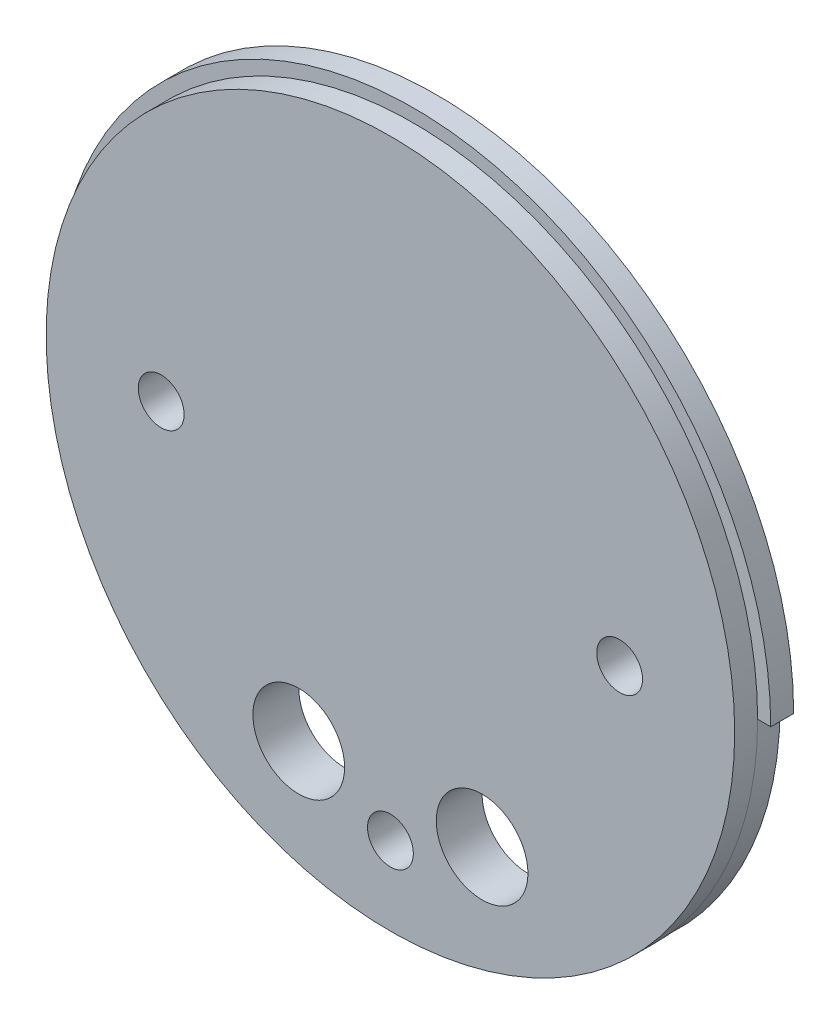
SolidWorks part; units mm, degrees
ref_plane "Front Plane" through (0, 0, 0) normal (0, 0, 1) x (1, 0, 0)
ref_plane "Top Plane" through (0, 0, 0) normal (0, 1, 0) x (1, 0, 0)
ref_plane "Right Plane" through (0, 0, 0) normal (1, 0, 0) x (0, 0, -1)
sketch "Sketch1" plane through (0, 0, 0) normal (0, 0, 1) x (1, 0, 0)
  circle A0 centre (0, 0) radius 49.5046
  dimension "D1" = 99.0092
extrude "Boss-Extrude1" add sketch "Sketch1" along normal blind 3.175
sketch "Sketch2" plane through (0, 0, 3.175) normal (0, 0, 1) x (1, 0, 0)
  circle A0 centre (0, 0) radius 47.6885
  dimension "D1" = 95.377
extrude "Boss-Extrude2" add sketch "Sketch2" along normal blind 3.175
sketch "Sketch3" plane through (0, 0, 6.35) normal (0, 0, 1) x (1, 0, 0)
  line L0 (-7.9375, -31.2354) -> (7.9375, -31.2354) construction
  circle A0 centre (-31.75, 0) radius 3.175
  circle A1 centre (31.75, 0) radius 3.175
  circle A2 centre (-12.7, -31.2354) radius 6.35
  circle A3 centre (-12.7, -31.2354) radius 13.97 construction
  circle A4 centre (-12.7, -31.2354) radius 4.7625 construction
  circle A5 centre (0, 0) radius 47.6885 construction
  circle A6 centre (12.7, -31.2354) radius 6.35
  circle A7 centre (12.7, -31.2354) radius 13.97 construction
  circle A8 centre (-12.7, -31.2354) radius 12.7 construction
  circle A9 centre (12.7, -31.2354) radius 12.7 construction
  circle A10 centre (12.7, -31.2354) radius 4.7625 construction
  circle A11 centre (0, -36.8046) radius 3.175
  circle A12 centre (0, 0) radius 49.5046 construction
  point P20 (0, -49.5046)
  dimension "D1" = 6.35
  dimension "D2" = 6.35
  dimension "D5" = 12.7
  dimension "D6" = 27.94
  dimension "D7" = 12.7
  dimension "D8" = 27.94
  dimension "D9" = 25.4
  dimension "D10" = 25.4
  dimension "D11" = 9.525
  dimension "D12" = 9.525
  dimension "D13" = 6.35
  dimension "D3" = 63.5
  dimension "D4" = 31.75
  dimension "D14" = 12.7
extrude "Cut-Extrude1" cut sketch "Sketch3" against normal through all
sketch "Sketch4" plane through (0, 0, 3.175) normal (0, 0, 1) x (1, 0, 0)
  line L0 (-50.165, 0) -> (-47.625, 0)
  line L1 (47.625, 0) -> (50.165, 0)
  arc A0 (-50.165, 0) -> (50.165, 0) centre (0, 0) ccw
  arc A1 (-47.625, 0) -> (47.625, 0) centre (0, 0) ccw
extrude "Cut-Extrude2" cut sketch "Sketch4" against normal through all
